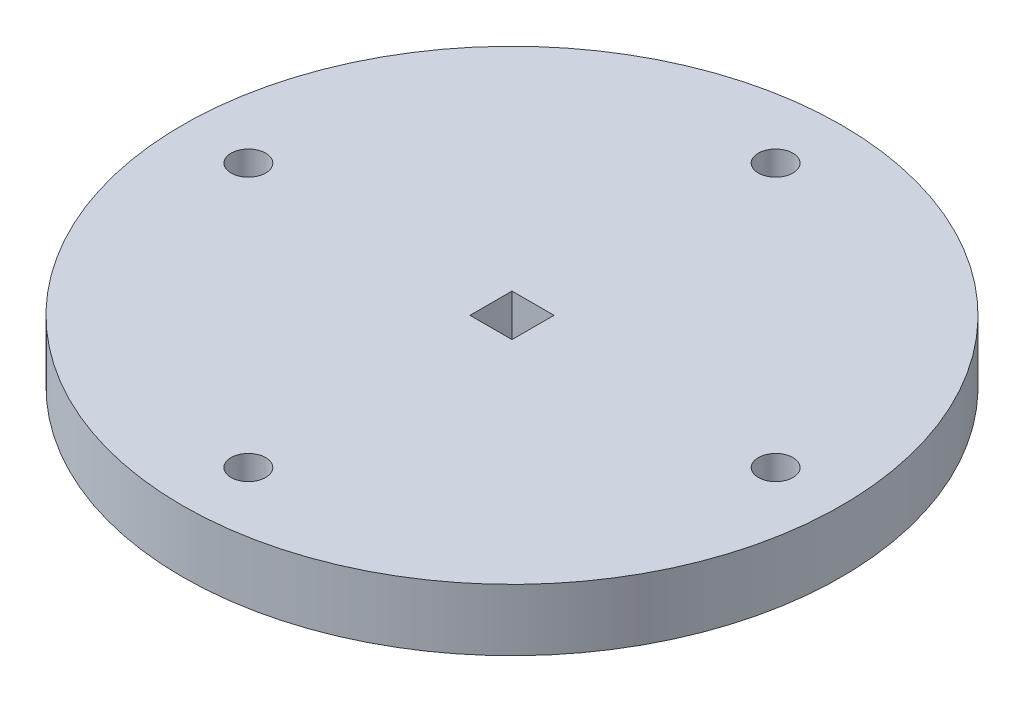
SolidWorks part; units mm, degrees
ref_plane "Front" through (0, 0, 0) normal (0, 0, 1) x (1, 0, 0)
ref_plane "Top" through (0, 0, 0) normal (0, 1, 0) x (1, 0, 0)
ref_plane "Right" through (0, 0, 0) normal (1, 0, 0) x (0, 0, -1)
sketch "Sketch2" plane through (0, 0, 0) normal (0, 1, 0) x (1, 0, 0)
  circle A0 centre (0, 0) radius 50.8
  dimension "D1" = 101.6
extrude "Boss-Extrude1" add sketch "Sketch2" along normal blind 9.525
sketch "Sketch3" plane through (0, 9.525, 0) normal (0, 1, 0) x (1, 0, 0)
  circle A2 centre (0, -40.64) radius 2.667
  circle A3 centre (0, 0) radius 40.64
  circle A4 centre (0, 0) radius 40.64 construction
  circle A5 centre (-40.64, 0) radius 2.667
  circle A6 centre (0, 40.64) radius 2.667
  circle A7 centre (40.64, 0) radius 2.667
  circle A8 centre (0, 0) radius 50.8 construction
  dimension "D2" = 5.334
  dimension "D1" = 10.16
  dimension "D3" = 4
extrude "Cut-Extrude1" cut sketch "Sketch3" against normal through all
sketch "Sketch4" plane through (0, 9.525, 0) normal (0, 1, 0) x (1, 0, 0)
  line L1 (3.2385, 3.2385) -> (-3.2385, 3.2385)
  line L2 (3.2385, 3.2385) -> (3.2385, -3.2385)
  line L3 (3.2385, -3.2385) -> (-3.2385, -3.2385)
  line L4 (-3.2385, 3.2385) -> (-3.2385, -3.2385)
  line L5 (3.2385, 3.2385) -> (-3.2385, -3.2385) construction
  line L6 (3.2385, -3.2385) -> (-3.2385, 3.2385) construction
  point P0 (0, 0)
  dimension "D1" = 6.477
extrude "Cut-Extrude2" cut sketch "Sketch4" against normal through all
